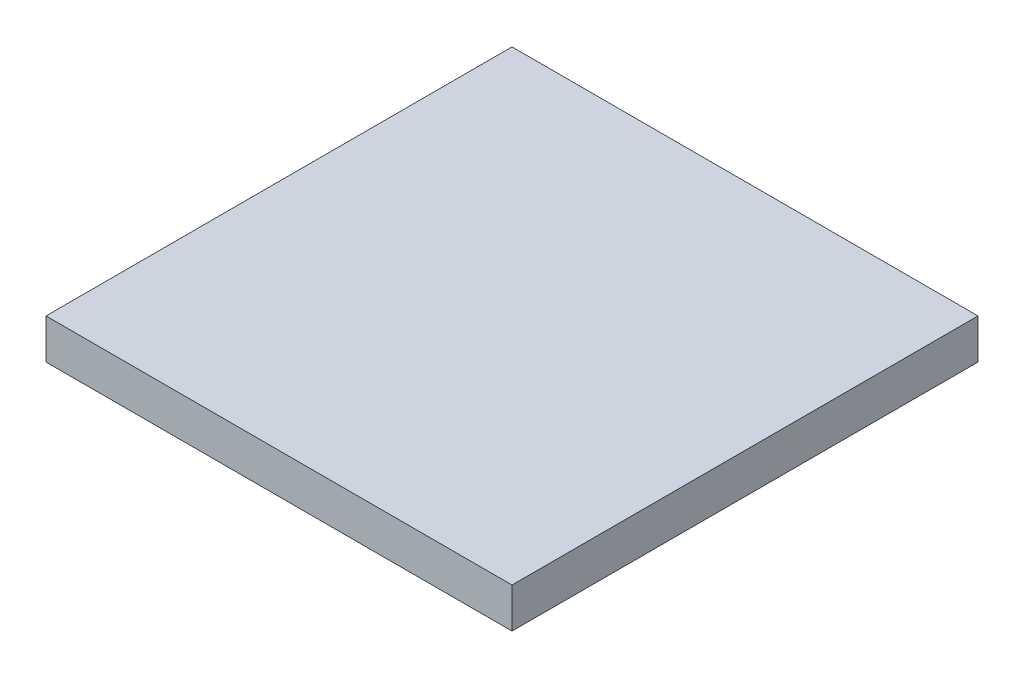
SolidWorks part; units mm, degrees
ref_plane "Front Plane" through (0, 0, 0) normal (0, 0, 1) x (1, 0, 0)
ref_plane "Top Plane" through (0, 0, 0) normal (0, 1, 0) x (1, 0, 0)
ref_plane "Right Plane" through (0, 0, 0) normal (1, 0, 0) x (0, 0, -1)
sketch "Sketch1" plane through (0, 0, 0) normal (0, 1, 0) x (1, 0, 0)
  line L1 (-17.5, 17.5) -> (17.5, 17.5)
  line L2 (-17.5, 17.5) -> (-17.5, -17.5)
  line L3 (-17.5, -17.5) -> (17.5, -17.5)
  line L4 (17.5, 17.5) -> (17.5, -17.5)
  line L5 (-17.5, 17.5) -> (17.5, -17.5) construction
  line L6 (-17.5, -17.5) -> (17.5, 17.5) construction
  point P0 (0, 0)
  dimension "D1" = 35
extrude "Boss-Extrude1" add sketch "Sketch1" along normal blind 3
